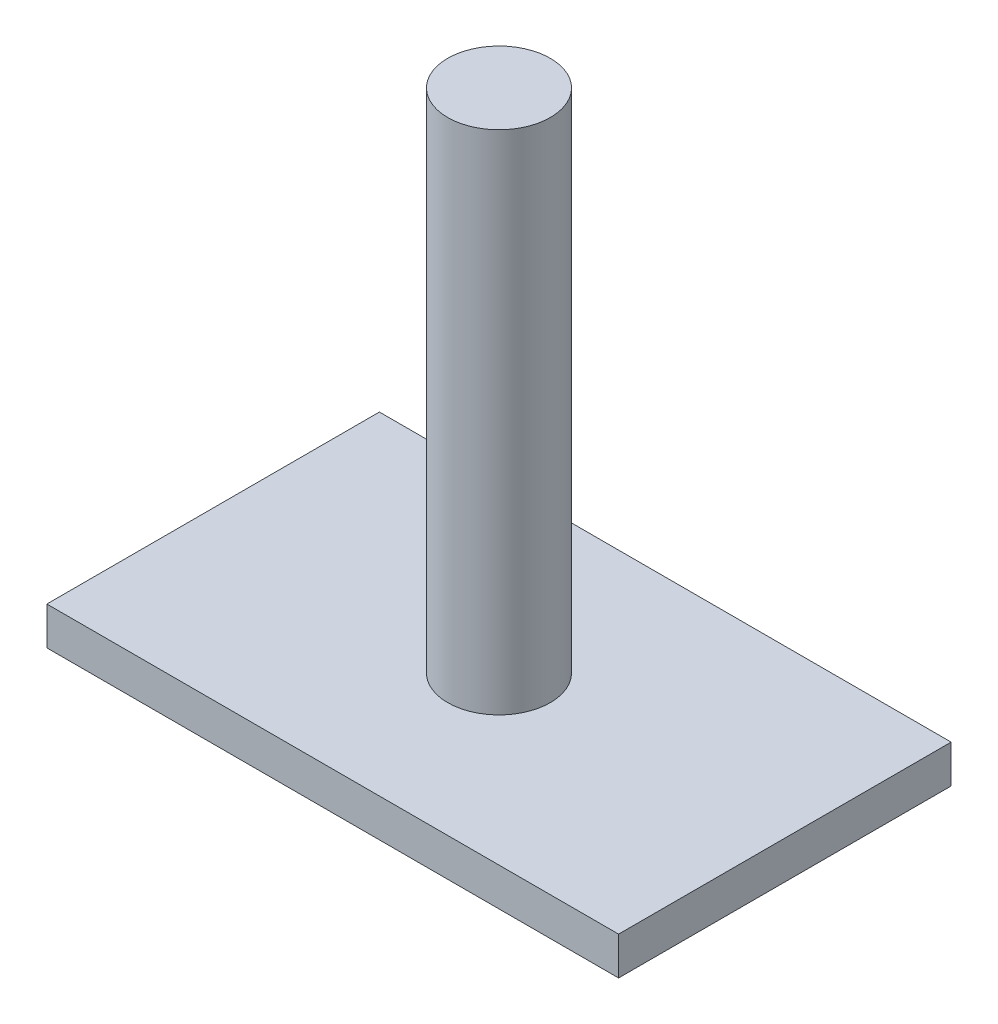
SolidWorks part; units mm, degrees
ref_plane "Front Plane" through (0, 0, 0) normal (0, 0, 1) x (1, 0, 0)
ref_plane "Top Plane" through (0, 0, 0) normal (0, 1, 0) x (1, 0, 0)
ref_plane "Right Plane" through (0, 0, 0) normal (1, 0, 0) x (0, 0, -1)
sketch "Sketch1" plane through (0, 0, 0) normal (0, 1, 0) x (1, 0, 0)
  circle A0 centre (0, 0) radius 4.05
  point P3 (0, 0)
  dimension "D1" = 8.1
extrude "Boss-Extrude1" add sketch "Sketch1" along normal blind 40
sketch "Sketch2" plane through (0, 0, 0) normal (0, -1, 0) x (1, 0, 0)
  line L1 (-22.564, 13.1244) -> (22.564, 13.1244)
  line L2 (-22.564, 13.1244) -> (-22.564, -13.1244)
  line L3 (-22.564, -13.1244) -> (22.564, -13.1244)
  line L4 (22.564, 13.1244) -> (22.564, -13.1244)
  line L5 (-22.564, 13.1244) -> (22.564, -13.1244) construction
  line L6 (-22.564, -13.1244) -> (22.564, 13.1244) construction
  point P0 (0, 0)
extrude "Boss-Extrude2" add sketch "Sketch2" along normal blind 3
